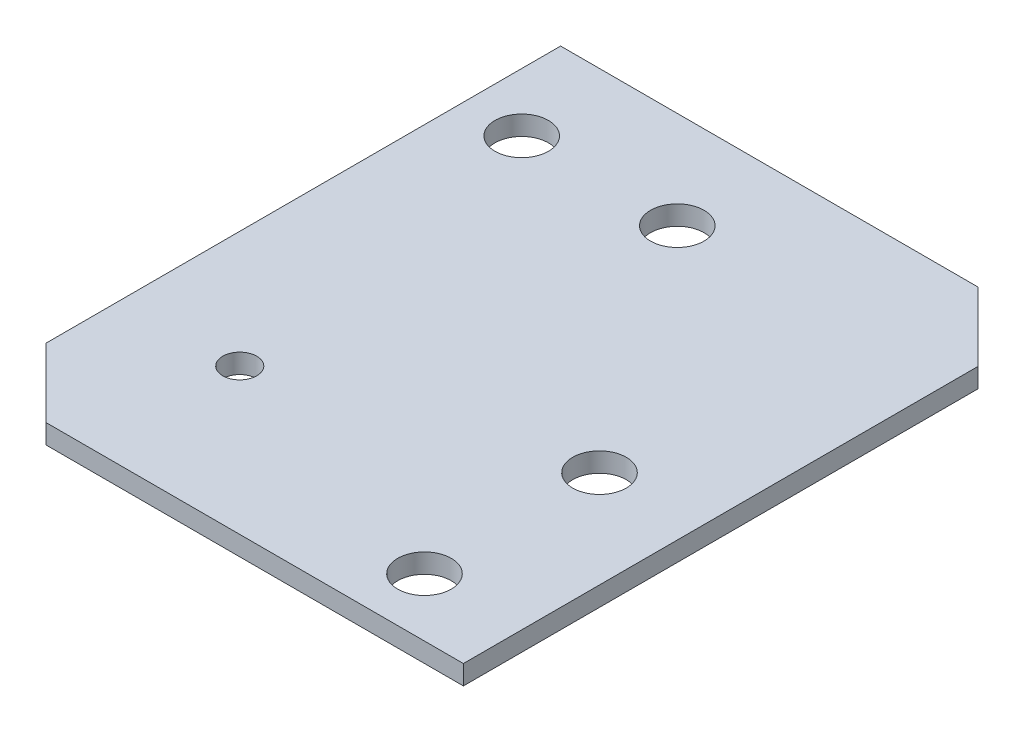
SolidWorks part; units mm, degrees
ref_plane "前视基准面" through (0, 0, 0) normal (0, 0, 1) x (1, 0, 0)
ref_plane "上视基准面" through (0, 0, 0) normal (0, 1, 0) x (1, 0, 0)
ref_plane "右视基准面" through (0, 0, 0) normal (1, 0, 0) x (0, 0, -1)
sketch "草图1" plane through (0, 0, 0) normal (0, 1, 0) x (1, 0, 0)
  line L0 (0, 0) -> (50, 0)
  line L1 (50, 0) -> (50, 60)
  line L3 (50, 60) -> (0, 60)
  line L4 (0, 60) -> (0, 0)
  dimension "D3" = 50
  dimension "D4" = 60
extrude "凸台-拉伸1" add sketch "草图1" along normal blind 2
sketch "草图2" plane through (0, 2, 0) normal (0, 1, 0) x (1, 0, 0)
  line L1 (0, 0) -> (50, 0) construction
  line L2 (50, 0) -> (50, 60) construction
  line L3 (50, 60) -> (0, 60) construction
  line L4 (0, 60) -> (0, 0) construction
  line L6 (0, 7.0711) -> (7.0711, 0)
  line L7 (0, 0) -> (0, 7.0711)
  line L8 (0, 0) -> (7.0711, 0)
  line L9 (50, 60) -> (50, 52.9289)
  line L10 (50, 0) -> (50, 60) construction
  line L11 (50, 52.9289) -> (42.9289, 60)
  line L12 (50, 60) -> (0, 60) construction
  line L13 (42.9289, 60) -> (50, 60)
  circle A1 centre (6, 50) radius 2.75
  circle A3 centre (40, 6) radius 2.75
  circle A4 centre (12, 15) radius 1.75
  circle A6 centre (40, 24) radius 2.75
  circle A7 centre (22, 50) radius 2.75
  dimension "D1" = 3.5
  dimension "D2" = 5.5
  dimension "D3" = 10
  dimension "D4" = 5.5
  dimension "D12" = 45
  dimension "D5" = 6
  dimension "D6" = 6
  dimension "D7" = 15
  dimension "D8" = 10
  dimension "D9" = 12
  dimension "D13" = 10
  dimension "D14" = 10
  dimension "D15" = 45
  dimension "D11" = 2
  dimension "D10" = 2
extrude "切除-拉伸1" cut sketch "草图2" against normal through all
sketch "草图3" plane through (0, 0, 0) normal (0, 1, 0) x (1, 0, 0)
  line L0 (30, 80) -> (80, 30) construction
